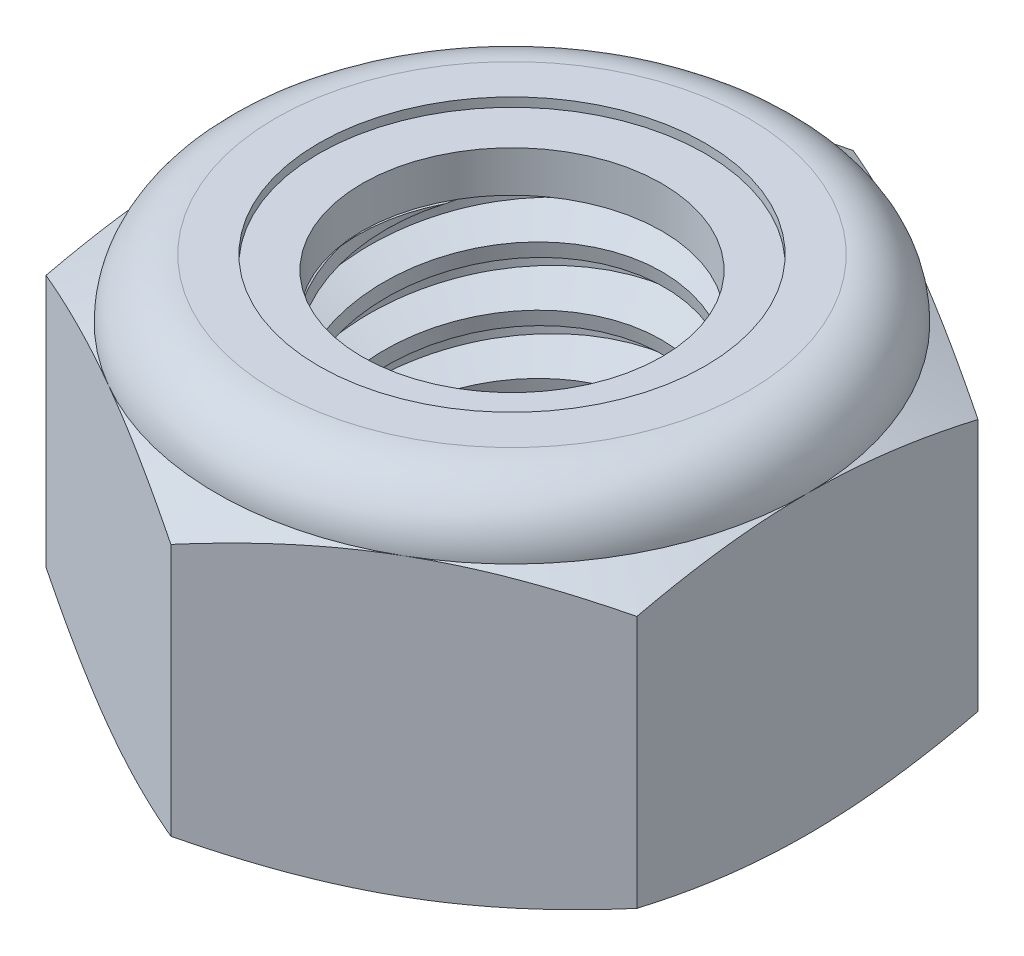
SolidWorks part; units mm, degrees
ref_plane "Front" through (0, 0, 0) normal (0, 0, 1) x (1, 0, 0)
ref_plane "Top" through (0, 0, 0) normal (0, 1, 0) x (1, 0, 0)
ref_plane "Right" through (0, 0, 0) normal (1, 0, 0) x (0, 0, -1)
sketch "Sketch1" plane through (0, 0, 0) normal (0, 1, 0) x (1, 0, 0)
  line L1 (0, 5.7735) -> (-5, 2.8868)
  line L2 (-5, 2.8868) -> (-5, -2.8868)
  line L3 (-5, -2.8868) -> (0, -5.7735)
  line L4 (0, -5.7735) -> (5, -2.8868)
  line L5 (5, -2.8868) -> (5, 2.8868)
  line L6 (5, 2.8868) -> (0, 5.7735)
  circle A0 centre (0, 0) radius 5 construction
  dimension "Hex Flats" = 10
extrude "Extrude1" add sketch "Sketch1" along normal blind 6
sketch "Sketch2" plane through (0, 0, 0) normal (1, 0, 0) x (0, 0, -1)
  line L0 (-3, 0) -> (-3, 6) construction
  line L1 (0, 0) -> (3, 0)
  line L2 (0, 0) -> (0, 6)
  line L3 (0, 6) -> (3, 6)
  line L4 (3, 0) -> (3, 6)
  line L5 (-2.8868, 6) -> (2.8868, 6) construction
  line L7 (0, -3) -> (0, 0) construction
  dimension "Thread Dia" = 6
revolve "Revolve1" add sketch "Sketch2" angle 360 about L7
sketch "Sketch3" plane through (0, 0, 0) normal (1, 0, 0) x (0, 0, -1)
  line L0 (3, 6) -> (-3, 6) construction
  line L1 (-3, 6) -> (-3, 5) construction
  line L2 (-3, 5) -> (3, 6) construction
  line L3 (3, 6) -> (3.0205, 5.8767) construction
  line L4 (3.0205, 5.8767) -> (3.1644, 5.0136)
  line L5 (3.1644, 5.0136) -> (2.5791, 5.2329)
  line L6 (2.5791, 5.2329) -> (2.538, 5.4795)
  line L7 (2.538, 5.4795) -> (3.0205, 5.8767)
  line L8 (2.5586, 5.3562) -> (3.0925, 5.4452) construction
  line L9 (3, 6) -> (3, 5.4297) construction
  line L10 (3, 5.4297) -> (-3, 4.4297) construction
  line L11 (-3, 4.4297) -> (-3, 5) construction
  line L12 (-0.1784, 6) -> (0.1784, 3.8595) construction
  line L13 (-3, 0) -> (-3, 6) construction
  line L14 (0, 6) -> (3, 6) construction
  line L15 (3, 0) -> (3, 6) construction
  point P13 (0, 4.9297)
  dimension "D1" = 0.125
  dimension "D2" = 0.25
  dimension "Thread Pitch" = 1
  dimension "D4" = 60
  dimension "D5" = 1
revolve "Cut-Revolve1" cut sketch "Sketch3" angle 360 about L12
pattern_linear "LPattern1" count 6 spacing 1 along (0, -1, 0) count 2 spacing 1 along (0, 1, 0) of "Cut-Revolve1"
sketch "Sketch4" plane through (0, 0, 0) normal (1, 0, 0) x (0, 0, -1)
  line L0 (0, 6) -> (3, 6)
  line L1 (3, 6) -> (2.538, 5.7846)
  line L2 (2.538, 5.7846) -> (2.538, 0.2154)
  line L3 (2.538, 0.2154) -> (3, 0)
  line L4 (3, 0) -> (0, 0)
  line L5 (0, 0) -> (0, 6)
  line L6 (3, 0) -> (3, 6) construction
  line L7 (0, 6) -> (3, 6) construction
  line L8 (0, 0) -> (3, 0) construction
  line L9 (0, 0) -> (0, 6) construction
  line L10 (0, 6) -> (0, 6.5097) construction
  dimension "D1" = 25
revolve "Cut-Revolve2" cut sketch "Sketch4" angle 360 about L10
combine bodies "Combine1" operation type subtract main body 112 bodies to subtract 111
sketch "Sketch5" plane through (0, 0, 0) normal (1, 0, 0) x (0, 0, -1)
  line L0 (0, 0) -> (5, 0)
  line L1 (5, 0) -> (5.7735, 0.3607)
  line L2 (5.7735, 0.3607) -> (5.7735, 4.6393)
  line L3 (5.7735, 4.6393) -> (5, 5)
  line L4 (4, 6) -> (4, 7.27)
  line L5 (4, 7.27) -> (7.0435, 7.27)
  line L6 (7.0435, 7.27) -> (7.0435, -1.27)
  line L7 (7.0435, -1.27) -> (0, -1.27)
  line L8 (0, -1.27) -> (0, 0)
  line L9 (5, 5) -> (5, 0) construction
  line L10 (0, 0) -> (3, 0) construction
  line L13 (5.7735, 2.5) -> (7.0435, 2.5) construction
  line L14 (5.7735, 6) -> (5.7735, 0) construction
  line L15 (0, 0) -> (0, 7.27) construction
  line L20 (0, 7.27) -> (4, 7.27) construction
  line L22 (0, 6) -> (3, 6) construction
  arc A0 (5, 5) -> (4, 6) centre (4, 5) ccw
  dimension "D4" = 1
  dimension "D1" = 25
  dimension "D2" = 1.27
  dimension "D3" = 6
revolve "Cut-Revolve3" cut sketch "Sketch5" angle 360 about L15
sketch "Sketch6" plane through (0, 0, 0) normal (1, 0, 0) x (0, 0, -1)
  line L0 (0, 5) -> (4.8476, 5)
  line L1 (4, 5.8476) -> (3.269, 5.8476)
  line L2 (0, 7.27) -> (0, 5)
  line L3 (3.269, 7.27) -> (0, 7.27)
  line L4 (0, 7.27) -> (4, 7.27) construction
  line L5 (0, 0) -> (0, 7.27) construction
  line L6 (0, 7.27) -> (0, 44.323) construction
  line L7 (3.269, 5.8476) -> (3.269, 7.27)
  line L8 (4, 6) -> (4, 5.8476) construction
  line L9 (3.269, 5.8476) -> (2.538, 5.8476) construction
  line L10 (2.538, 5.8476) -> (2.538, 5.7846) construction
  arc A0 (4.8476, 5) -> (4, 5.8476) centre (4, 5) ccw
  arc A1 (5, 5) -> (4, 6) centre (4, 5) ccw construction
  dimension "D1" = 0.1524
revolve "Cut-Revolve4" cut sketch "Sketch6" angle 360 about L6
sketch "Sketch7" plane through (0, 0, 0) normal (1, 0, 0) x (0, 0, -1)
  line L0 (2.538, 5.0762) -> (4.7676, 5.0762)
  line L1 (4, 5.7714) -> (2.538, 5.7714)
  line L2 (2.538, 5.7714) -> (2.538, 5.0762)
  line L3 (2.538, 5.0762) -> (0, 5.0762) construction
  line L4 (0, 5.0762) -> (0, 5.7714) construction
  line L5 (0, 5.7714) -> (2.538, 5.7714) construction
  line L6 (2.538, 5.0762) -> (2.538, 5) construction
  line L7 (0, 5) -> (4.8476, 5) construction
  line L8 (4, 5.7714) -> (4, 5.8476) construction
  arc A0 (4.7676, 5.0762) -> (4, 5.7714) centre (4, 5) ccw
  arc A2 (4.8476, 5) -> (4, 5.8476) centre (4, 5) ccw construction
  dimension "D1" = 0.0762
revolve "Revolve2" add sketch "Sketch7" angle 360 about L4
equation "\"D1@Sketch3\"=\"Thread Pitch@Sketch3\"/8"
equation "\"D2@Sketch3\"=\"Thread Pitch@Sketch3\"/4"
equation "\"D5@Sketch3\"=\"Thread Pitch@Sketch3\""
equation "\"D4@LPattern1\"=\"Thread Pitch@Sketch3\""
equation "\"D3@LPattern1\"=\"Thread Pitch@Sketch3\""
equation "\"D1@LPattern1\"=\"Height@Extrude1\"/\"Thread Pitch@Sketch3\""
equation "\"D4@Sketch5\"=\"Height@Extrude1\"/6"
